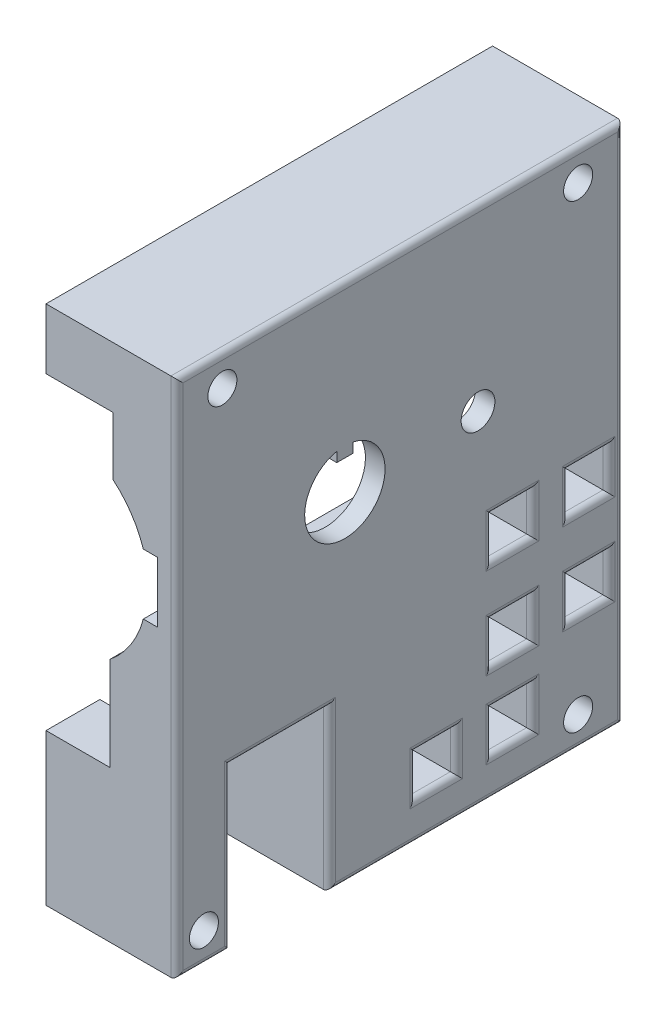
SolidWorks part; units mm, degrees
ref_plane "Front" through (0, 0, 0) normal (0, 0, 1) x (1, 0, 0)
ref_plane "Top" through (0, 0, 0) normal (0, 1, 0) x (1, 0, 0)
ref_plane "Right" through (0, 0, 0) normal (1, 0, 0) x (0, 0, -1)
sketch "Profile" plane through (0, 0, 0) normal (0, 0, 1) x (1, 0, 0)
  line L0 (-6.4407, -58.6279) -> (-6.4407, -33.6279)
  line L1 (-6.4407, -58.6279) -> (15.1893, -58.6279)
  line L2 (-6.4407, 17.4121) -> (-6.4407, 27.4121)
  line L3 (-6.4407, 27.4121) -> (15.1893, 27.4121)
  line L4 (15.1893, -58.6279) -> (15.1893, 27.4121)
  line L5 (-6.4407, -33.6279) -> (4.1393, -33.6279)
  line L6 (4.1393, -33.6279) -> (4.1393, -18.1379)
  line L7 (9.6313, -9.6379) -> (11.9493, -9.6379)
  line L8 (11.9493, -9.6379) -> (11.9493, 0.3621)
  line L9 (9.6293, 0.3621) -> (11.9493, 0.3621)
  line L10 (4.6093, 17.4121) -> (4.6093, 7.8121)
  line L11 (4.6093, 17.4121) -> (-6.4407, 17.4121)
  arc A0 (9.6293, 0.3621) -> (4.6093, 7.8121) centre (-5.8413, -4.6461) ccw
  arc A1 (4.1393, -18.1379) -> (9.6313, -9.6379) centre (-6.0948, -5.5013) ccw
  dimension "D14" = 16.261
  dimension "D17" = 16.261
  dimension "D2" = 10
  dimension "D3" = 2.32
  dimension "D4" = 2.318
  dimension "D5" = 9.6
  dimension "D6" = 11.05
  dimension "D7" = 15.49
  dimension "D8" = 10.58
  dimension "D9" = 25
  dimension "D10" = 21.63
  dimension "D11" = 86.04
  dimension "D12" = 21.63
  dimension "D13" = 10
  dimension "D15" = 23.99
  dimension "D16" = 5.492
extrude "ProfileExtrude" add sketch "Profile" along normal blind 73.76
sketch "HoseWindow" plane through (15.1893, 0, 0) normal (1, 0, 0) x (0, 0, -1)
  line L0 (-73.76, -58.6279) -> (0, -58.6279) construction
  line L1 (-64.87, -58.6279) -> (-48.58, -58.6279)
  line L2 (-64.87, -58.6279) -> (-64.87, -32.1279)
  line L3 (-64.87, -32.1279) -> (-48.58, -32.1279)
  line L4 (-48.58, -58.6279) -> (-48.58, -32.1279)
  line L5 (-73.76, -58.6279) -> (-73.76, 27.4121) construction
  dimension "D1" = 16.29
  dimension "D2" = 26.5
  dimension "D3" = 8.89
extrude "HoseWindowCut" cut sketch "HoseWindow" against normal through all
sketch "CageScrews" plane through (15.1893, 0, 0) normal (1, 0, 0) x (0, 0, -1)
  line L0 (-73.76, 27.4121) -> (0, 27.4121) construction
  line L1 (-73.76, -58.6279) -> (-73.76, 27.4121) construction
  line L2 (0, -58.6279) -> (0, 27.4121) construction
  line L3 (-48.58, -58.6279) -> (0, -58.6279) construction
  line L4 (-73.76, -58.6279) -> (-64.87, -58.6279) construction
  circle A0 centre (-66.26, 22.4121) radius 2.4
  circle A1 centre (-7.5, 22.4121) radius 2.4
  circle A2 centre (-7.5, -53.6279) radius 2.4
  circle A3 centre (-69.31, -53.6279) radius 2.4
  dimension "D1" = 4.8
  dimension "D2" = 4.8
  dimension "D3" = 4.8
  dimension "D4" = 4.8
  dimension "D5" = 5
  dimension "D6" = 7.5
  dimension "D7" = 7.5
  dimension "D8" = 5
  dimension "D9" = 5
  dimension "D10" = 7.5
  dimension "D11" = 5
  dimension "D12" = 4.45
extrude "CageScrewsCut" cut sketch "CageScrews" against normal through all
sketch "AxleHole" plane through (15.1893, 0, 0) normal (1, 0, 0) x (0, 0, -1)
  line L0 (-46.03, 2.3073) -> (-46.03, -9.2169) construction
  line L1 (-44.699, 2.3073) -> (-47.361, 2.3073)
  line L2 (-47.361, 2.3073) -> (-47.361, 3.9263)
  line L3 (-44.699, 2.3073) -> (-44.699, 3.9263)
  line L4 (-48.58, -58.6279) -> (0, -58.6279) construction
  line L5 (0, -58.6279) -> (0, 27.4121) construction
  arc A0 (-47.361, 3.9263) -> (-44.699, 3.9263) centre (-46.03, -2.5779) ccw
  dimension "D1" = 13.278
  dimension "D2" = 1.619
  dimension "D3" = 1.619
  dimension "D4" = 1.331
  dimension "D5" = 56.05
  dimension "D6" = 46.03
extrude "AxleHoleCut" cut sketch "AxleHole" against normal through all
sketch "SetScrews" plane through (15.1893, 0, 0) normal (1, 0, 0) x (0, 0, -1)
  line L0 (-46.03, -9.2169) -> (-46.03, -2.5779) construction
  circle A0 centre (-85.625, 3.1) radius 2.4263
  circle A1 centre (-24.0371, -2.0171) radius 2.7888
  arc A3 (-47.361, 3.9263) -> (-44.699, 3.9263) centre (-46.03, -2.5779) ccw construction
  dimension "D1" = 40
  dimension "D2" = 22
extrude "SetScrewsCut" cut sketch "SetScrews" against normal through all
sketch "Sketch1" plane through (15.1893, 0, 0) normal (1, 0, 0) x (0, 0, -1)
  line L0 (-21.7, -45.5779) -> (-21.7, -52.2779)
  line L1 (-21.7, -45.5779) -> (-15, -45.5779)
  line L2 (-21.7, -52.2779) -> (-15, -52.2779)
  line L3 (-15, -45.5779) -> (-15, -52.2779)
  line L4 (0, -58.6279) -> (0, 27.4121) construction
  line L5 (-48.58, -58.6279) -> (0, -58.6279) construction
  line L6 (-34.3, -45.5779) -> (-27.6, -45.5779)
  line L7 (-34.3, -52.2779) -> (-27.6, -52.2779)
  line L8 (-34.3, -45.5779) -> (-34.3, -52.2779)
  line L9 (-27.6, -45.5779) -> (-27.6, -52.2779)
  line L10 (-9.1, -32.8779) -> (-2.4, -32.8779)
  line L11 (-9.1, -39.5779) -> (-2.4, -39.5779)
  line L12 (-9.1, -32.8779) -> (-9.1, -39.5779)
  line L13 (-2.4, -32.8779) -> (-2.4, -39.5779)
  line L14 (-21.7, -32.8779) -> (-15, -32.8779)
  line L15 (-21.7, -39.5779) -> (-15, -39.5779)
  line L16 (-21.7, -32.8779) -> (-21.7, -39.5779)
  line L17 (-15, -32.8779) -> (-15, -39.5779)
  line L18 (-21.7, -45.5779) -> (-34.3, -45.5779) construction
  line L19 (-9.1, -17.8779) -> (-2.4, -17.8779)
  line L20 (-9.1, -24.5779) -> (-2.4, -24.5779)
  line L21 (-9.1, -17.8779) -> (-9.1, -24.5779)
  line L22 (-2.4, -17.8779) -> (-2.4, -24.5779)
  line L23 (-21.7, -17.8779) -> (-15, -17.8779)
  line L24 (-21.7, -24.5779) -> (-15, -24.5779)
  line L25 (-21.7, -17.8779) -> (-21.7, -24.5779)
  line L26 (-15, -17.8779) -> (-15, -24.5779)
  line L27 (-21.7, -32.8779) -> (-9.1, -32.8779) construction
  line L42 (-34.3, -32.8779) -> (-27.6, -32.8779) [skipped]
  line L43 (-34.3, -39.5779) -> (-27.6, -39.5779) [skipped]
  line L44 (-34.3, -32.8779) -> (-34.3, -39.5779) [skipped]
  line L45 (-27.6, -32.8779) -> (-27.6, -39.5779) [skipped]
  dimension "D1" = 15
  dimension "D2" = 6.7
  dimension "D3" = 6.7
  dimension "D4" = 6.35
  dimension "D5" = 12.6
  dimension "D6" = 12.6
extrude "Cut-Extrude1" cut sketch "Sketch1" against normal through all
fillet "Fillet1" radius 1 32 edges at (15.1893, -48.9279, 21.7) (15.1893, -52.2779, 18.35) (15.1893, -48.9279, 15) (15.1893, -45.5779, 18.35) (15.1893, -58.6279, 69.315) (15.1893, -45.3779, 64.87) (15.1893, -32.1279, 56.725) (15.1893, -45.3779, 48.58) (15.1893, -58.6279, 24.29) (15.1893, -15.6079, 0) (15.1893, 27.4121, 36.88) (15.1893, -15.6079, 73.76) (15.1893, -24.5779, 5.75) (15.1893, -21.2279, 2.4) (15.1893, -17.8779, 5.75) (15.1893, -21.2279, 9.1) (15.1893, -21.2279, 15) (15.1893, -17.8779, 18.35) (15.1893, -21.2279, 21.7) (15.1893, -24.5779, 18.35) (15.1893, -39.5779, 5.75) (15.1893, -36.2279, 2.4) (15.1893, -32.8779, 5.75) (15.1893, -36.2279, 9.1) (15.1893, -36.2279, 15) (15.1893, -32.8779, 18.35) (15.1893, -36.2279, 21.7) (15.1893, -39.5779, 18.35) (15.1893, -52.2779, 30.95) (15.1893, -48.9279, 27.6) (15.1893, -45.5779, 30.95) (15.1893, -48.9279, 34.3)
equation "\"CageRightBottomEdge\"=21.63mm"
equation "\"CageRightTopEdge\"=21.63mm"
equation "\"CageHeight\"=86.04mm"
equation "\"CageLength\"=73.76mm"
equation "\"CageTopScrewClearance\"=10mm"
equation "\"CageRightTopDepth\"= 11.05mm"
equation "\"CageRightBottomDepth\"=10.58mm"
equation "\"CageRightTopHeight\"=9.6mm"
equation "\"CageRightBottomHeight\"=15.49mm"
equation "\"CageRightTopChannelDepth\"=2.32mm"
equation "\"CageRightBottomChannelDepth\"=2.318mm"
equation "\"CageRightChannelHeight\"=10mm"
equation "\"CageChamberRadius\"=16.261mm"
equation "\"CageChanRelHeight\"=23.99mm"
equation "\"CageChanRelDepth\"=5.492mm"
equation "\"D2@Profile\" = \"CageRightChannelHeight\""
equation "\"D4@Profile\" = \"CageRightBottomChannelDepth\""
equation "\"D3@Profile\" = \"CageRightTopChannelDepth\""
equation "\"D5@Profile\" = \"CageRightTopHeight\""
equation "\"D7@Profile\" = \"CageRightBottomHeight\""
equation "\"CageBottomScrewClearance\"=25mm"
equation "\"D9@Profile\" = \"CageBottomScrewClearance\""
equation "\"D13@Profile\" = \"CageTopScrewClearance\""
equation "\"D8@Profile\" = \"CageRightBottomDepth\""
equation "\"D6@Profile\" = \"CageRightTopDepth\""
equation "\"D10@Profile\" = \"CageRightBottomEdge\""
equation "\"D12@Profile\" = \"CageRightTopEdge\""
equation "\"D11@Profile\" = \"CageHeight\""
equation "\"D15@Profile\" = \"CageChanRelHeight\""
equation "\"D16@Profile\" = \"CageChanRelDepth\""
equation "\"D17@Profile\" = \"CageChamberRadius\""
equation "\"D14@Profile\" = \"CageChamberRadius\""
equation "\"D1@ProfileExtrude\" = \"CageLength\""
equation "\"CageScrewDiameter\"=4.8mm"
equation "\"CageSetScrewDiameter\"=3.5mm"
equation "\"CageAxleRadius\"=6.639mm"
equation "\"CageAxleKeyHeight\"=1.619mm"
equation "\"CageAxleKeyWidth\"=2.662mm"
equation "\"CageHoseWindowWidth\"=16.29mm"
equation "\"CageHoseWindowHeight\"=26.5mm"
equation "\"CageHoseWindow-Edge\"=8.89mm"
equation "\"CageScrew-VerticalEdge\"=5.0mm"
equation "\"CageScrew-HorizontalEdge\"=7.5mm"
equation "\"CageScrew-HoseCornerScrewEdge\"=4.45mm"
equation "\"CageAxle-BottomEdge\"=56.05mm"
equation "\"CageAxle-FrontEdge\"=46.03mm"
equation "\"CageBackSetScrew-Axle\"=40mm"
equation "\"D1@HoseWindow\" = \"CageHoseWindowWidth\""
equation "\"D2@HoseWindow\" = \"CageHoseWindowHeight\""
equation "\"D3@HoseWindow\" = \"CageHoseWindow-Edge\""
equation "\"D6@CageScrews\"= \"CageScrew-HorizontalEdge\""
equation "\"D7@CageScrews\"= \"CageScrew-HorizontalEdge\""
equation "\"D10@CageScrews\"= \"CageScrew-HorizontalEdge\""
equation "\"D12@CageScrews\"= \"CageScrew-HoseCornerScrewEdge\""
equation "\"D5@CageScrews\"= \"CageScrew-VerticalEdge\""
equation "\"D8@CageScrews\"= \"CageScrew-VerticalEdge\""
equation "\"D11@CageScrews\"= \"CageScrew-VerticalEdge\""
equation "\"D9@CageScrews\"= \"CageScrew-VerticalEdge\""
equation "\"D1@CageScrews\"= \"CageScrewDiameter\""
equation "\"D2@CageScrews\"= \"CageScrewDiameter\""
equation "\"D4@CageScrews\"= \"CageScrewDiameter\""
equation "\"D3@CageScrews\"= \"CageScrewDiameter\""
equation "\"D1@AxleHole\" = \"CageAxleRadius\" * 2"
equation "\"D3@AxleHole\" = \"CageAxleKeyHeight\""
equation "\"D2@AxleHole\" = \"CageAxleKeyHeight\""
equation "\"D4@AxleHole\"= \"CageAxleKeyWidth\" / 2"
equation "\"D6@AxleHole\" = \"CageAxle-FrontEdge\""
equation "\"D5@AxleHole\" = \"CageAxle-BottomEdge\""
equation "\"D2@SetScrews\" = \"CageFrontSetScrew-Axle\""
equation "\"CageFrontSetScrew-Axle\"=22mm"
equation "\"D1@SetScrews\" = \"CageBackSetScrew-Axle\""
equation "\"TriggerSlot-FrontEdge\"=15mm"
equation "\"D1@Sketch1\" = \"TriggerSlot-FrontEdge\""
equation "\"TriggerSlotSize\"=6.7mm"
equation "\"D2@Sketch1\" = \"TriggerSlotSize\""
equation "\"D3@Sketch1\" = \"TriggerSlotSize\""
equation "\"TriggerSlot-BottomEdge\"=6.35mm"
equation "\"D4@Sketch1\" = \"TriggerSlot-BottomEdge\""
equation "\"CageLeftBottomEdge\"=22.11mm"
equation "\"CageLeftTopEdge\"=22.11mm"
equation "\"CageLeftTopDepth\"= 11.65mm"
equation "\"CageLeftBottomDepth\"=11.11mm"
equation "\"CageLeftTopHeight\"=8.56175mm"
equation "\"CageLeftBottomHeight\"=16mm"
equation "\"CageLeftTopChannelDepth\"=2.41908mm"
equation "\"CageLeftBottomChannelDepth\"=2.588mm"
equation "\"CageLeftChannelHeight\"=11.7mm"
equation "\"CageVelocityWindow-BackEdge\"=34.8mm"
equation "\"CageVelocityWindow-BottomEdge\"=27.55mm"
equation "\"CageVelocityWindowHeight\"=22.29mm"
equation "\"CageVelocityWindowWidth\"=12.61mm"
equation "\"vigorwidth\"= 0.472441in"
equation "\"vigorflangewidth\"= 0.731102in"
equation "\"vigorflangelength\"= 0.131102in"
equation "\"vigorscrewsize\"= 0.066535in"
equation "\"vigorholeoffsetwid\"= 0.0646653in"
equation "\"vigorholeoffsetlen\"= 0.065551in"
equation "\"vigorflangedepth\"= 0.0901575in"
equation "\"vigordiscdepth\"= 0.0492126in"
equation "\"vigormotordepth\"= 1.12362in"
equation "\"vigortipdepth\"= 0.259055in"
equation "\"vigoraxlewidth\"= 0.173622in"
equation "\"vigorcutlen\"= 0.0480315in"
equation "\"vigoraxledepth\"= 0.159055in"
equation "\"TriggerRackOffset\"=.236224in"
equation "\"TriggerSlotSizeInt\"=.25in"
equation "\"MotorMountLegLength\"=.25in"
equation "\"GearOffset\"=.264907in"
equation "\"TriggerSlotSpacing\"=.25in"
equation "\"TriggerMiniSlotWidth\"=3.5mm"
equation "\"TriggerRackWidth\"=6.5mm"
equation "\"TGMGearFaceDiameter\"=24.40mm"
equation "\"TGMCylinderLength\"=15.00mm"
equation "\"TGMScrewHole-Center\"=8.70mm"
equation "\"TGMScrewHoleDiameter\"=5.04mm"
equation "\"TGMCenterHoleDiameter\"=9.50mm"
equation "\"TGMShaftCollarSideLength\"=19.00mm"
equation "\"TGMShaftCollarDockingDepth\"=7.00mm"
equation "\"whitemotordepth\"=11.27mm"
equation "\"whitemotorbackdepth\"=3.845mm"
equation "\"whitemotoraxledepth\" = 3.5mm"
equation "\"whitemotoraxleoffset\"=11.4mm"
equation "\"whitemotorwidth\"=12.07mm"
equation "\"whitemotorheight\"=16.68mm"
equation "\"whitemotorcylinderlength\" =13.04mm"
equation "\"whitemotorcylinderradius\"=3.845mm"
equation "\"whitemotorcylinderoffset\"=2.35mm"
equation "\"whitemotorcutoutlength\"=1.88mm"
equation "\"whitemotorouterrad\"=5mm"
